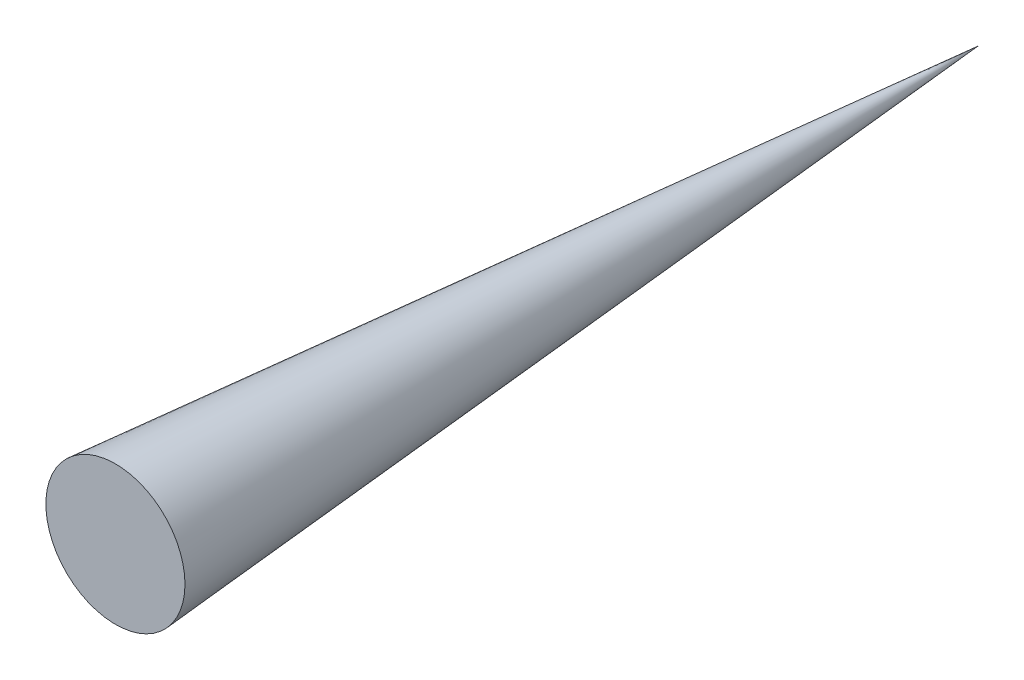
SolidWorks part; units mm, degrees
ref_plane "Front" through (0, 0, 0) normal (0, 0, 1) x (1, 0, 0)
ref_plane "Top" through (0, 0, 0) normal (0, 1, 0) x (1, 0, 0)
ref_plane "Right" through (0, 0, 0) normal (1, 0, 0) x (0, 0, -1)
sketch "Sketch1" plane through (0, 0, 0) normal (0, 1, 0) x (1, 0, 0)
  line L0 (0, 0) -> (-30, 0)
  line L1 (0, 0) -> (0, 372)
  line L2 (0, 372) -> (-30, 0)
  line L3 (0, -33.993) -> (0, 333.1348) construction
  dimension "D1" = 30
  dimension "D2" = 372
revolve "Revolve1" add sketch "Sketch1" angle 360 about L3
